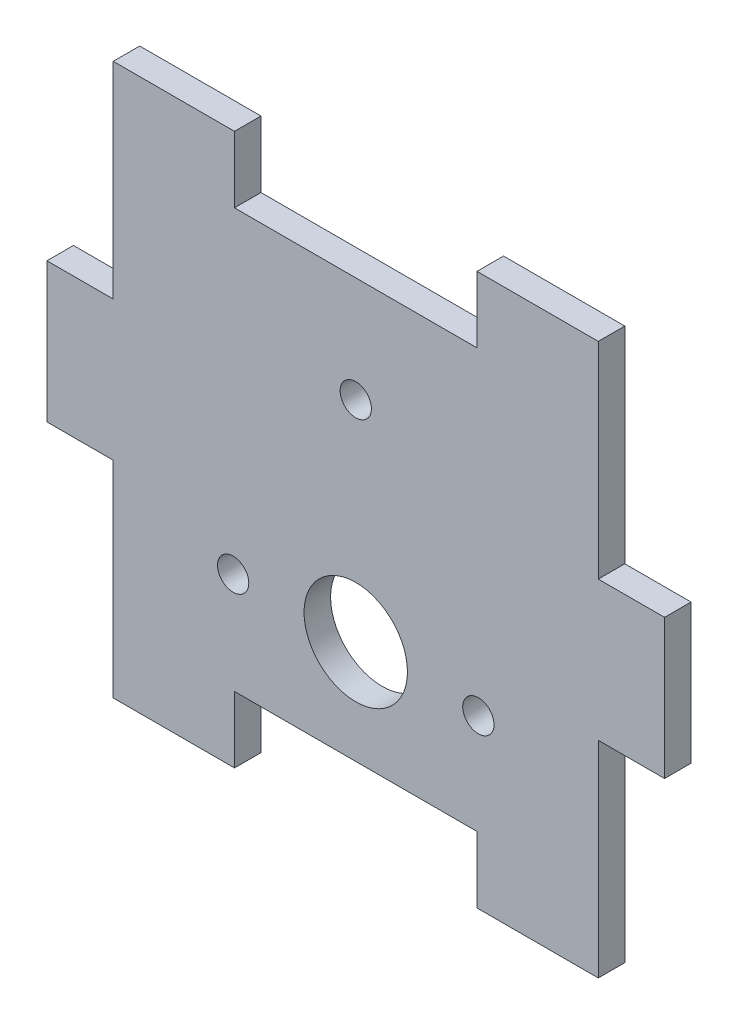
SolidWorks part; units mm, degrees
ref_plane "Front Plane" through (0, 0, 0) normal (0, 0, 1) x (1, 0, 0)
ref_plane "Top Plane" through (0, 0, 0) normal (0, 1, 0) x (1, 0, 0)
ref_plane "Right Plane" through (0, 0, 0) normal (1, 0, 0) x (0, 0, -1)
sketch "Sketch1" plane through (0, 0, 0) normal (0, 0, 1) x (1, 0, 0)
  line L1 (-23.241, -20.066) -> (23.241, -20.066)
  line L2 (-23.241, -20.066) -> (-23.241, 20.066)
  line L3 (-23.241, 20.066) -> (23.241, 20.066)
  line L4 (23.241, -20.066) -> (23.241, 20.066)
  line L5 (-23.241, -20.066) -> (23.241, 20.066) construction
  line L6 (-23.241, 20.066) -> (23.241, -20.066) construction
  point P0 (0, 0)
  dimension "D1" = 46.482
  dimension "D2" = 40.132
extrude "Boss-Extrude1" add sketch "Sketch1" along normal mid plane 2.54
sketch "Sketch2" plane through (0, 0, 1.27) normal (0, 0, 1) x (1, 0, 0)
  line L0 (-23.241, 20.066) -> (-23.241, -20.066) construction
  line L1 (-23.241, 20.066) -> (-11.6205, 20.066)
  line L2 (-23.241, 20.066) -> (-23.241, 26.416)
  line L3 (-23.241, 26.416) -> (-11.6205, 26.416)
  line L4 (-11.6205, 20.066) -> (-11.6205, 26.416)
  line L5 (23.241, 20.066) -> (11.6205, 20.066)
  line L6 (23.241, 20.066) -> (23.241, 26.416)
  line L7 (23.241, 26.416) -> (11.6205, 26.416)
  line L8 (11.6205, 20.066) -> (11.6205, 26.416)
  line L9 (-23.241, 6.6887) -> (-29.591, 6.6887)
  line L10 (-23.241, 6.6887) -> (-23.241, -6.6887)
  line L11 (-23.241, -6.6887) -> (-29.591, -6.6887)
  line L12 (-29.591, 6.6887) -> (-29.591, -6.6887)
  line L13 (23.241, -20.066) -> (23.241, 20.066) construction
  line L14 (23.241, -6.6887) -> (29.591, -6.6887)
  line L15 (23.241, -6.6887) -> (23.241, 6.6887)
  line L16 (23.241, 6.6887) -> (29.591, 6.6887)
  line L17 (29.591, -6.6887) -> (29.591, 6.6887)
  line L18 (-23.241, 20.066) -> (-23.241, 6.6887) construction
  line L19 (-23.241, -20.066) -> (-11.6205, -20.066)
  line L20 (-23.241, -20.066) -> (-23.241, -26.416)
  line L21 (-23.241, -26.416) -> (-11.6205, -26.416)
  line L22 (-11.6205, -20.066) -> (-11.6205, -26.416)
  line L23 (23.241, -20.066) -> (11.6205, -20.066)
  line L24 (23.241, -20.066) -> (23.241, -26.416)
  line L25 (23.241, -26.416) -> (11.6205, -26.416)
  line L26 (11.6205, -20.066) -> (11.6205, -26.416)
  line L27 (-23.241, -6.6887) -> (-23.241, -20.066) construction
  line L28 (-11.6205, -20.066) -> (0, -20.066) construction
  line L29 (23.241, -20.066) -> (23.241, -6.6887) construction
  line L30 (23.241, 6.6887) -> (23.241, 20.066) construction
  line L31 (0, 0) -> (0, 20.066) construction
  line L32 (23.241, 20.066) -> (-23.241, 20.066) construction
  line L33 (0, 20.066) -> (-11.6205, 20.066) construction
  line L34 (0, 20.066) -> (11.6205, 20.066) construction
  line L35 (0, 0) -> (0, -20.066) construction
  line L36 (0, -20.066) -> (11.6205, -20.066) construction
extrude "Boss-Extrude2" add sketch "Sketch2" against normal through all
sketch "Sketch3" plane through (0, 0, 1.27) normal (0, 0, 1) x (1, 0, 0)
  circle A0 centre (0, 9.954) radius 1.5 construction
  circle A1 centre (0, -10.16) radius 4.953 construction
  circle A2 centre (-11.75, -10.3976) radius 1.5 construction
  circle A3 centre (11.75, -10.3976) radius 1.5 construction
  circle A4 centre (0, 9.954) radius 1.5
  circle A5 centre (0, -10.16) radius 4.953
  circle A6 centre (-11.75, -10.3976) radius 1.5
  circle A7 centre (11.75, -10.3976) radius 1.5
extrude "Cut-Extrude1" cut sketch "Sketch3" against normal through all
equation "\"material\"=\"Acrylic@Platform.assembly\""
equation "\"D1@Boss-Extrude1\"=\"material\""
equation "\"MDF\"=\"GMaterial@Platform.assembly\""
equation "\"material@Sketch2\" = \"MDF\""
